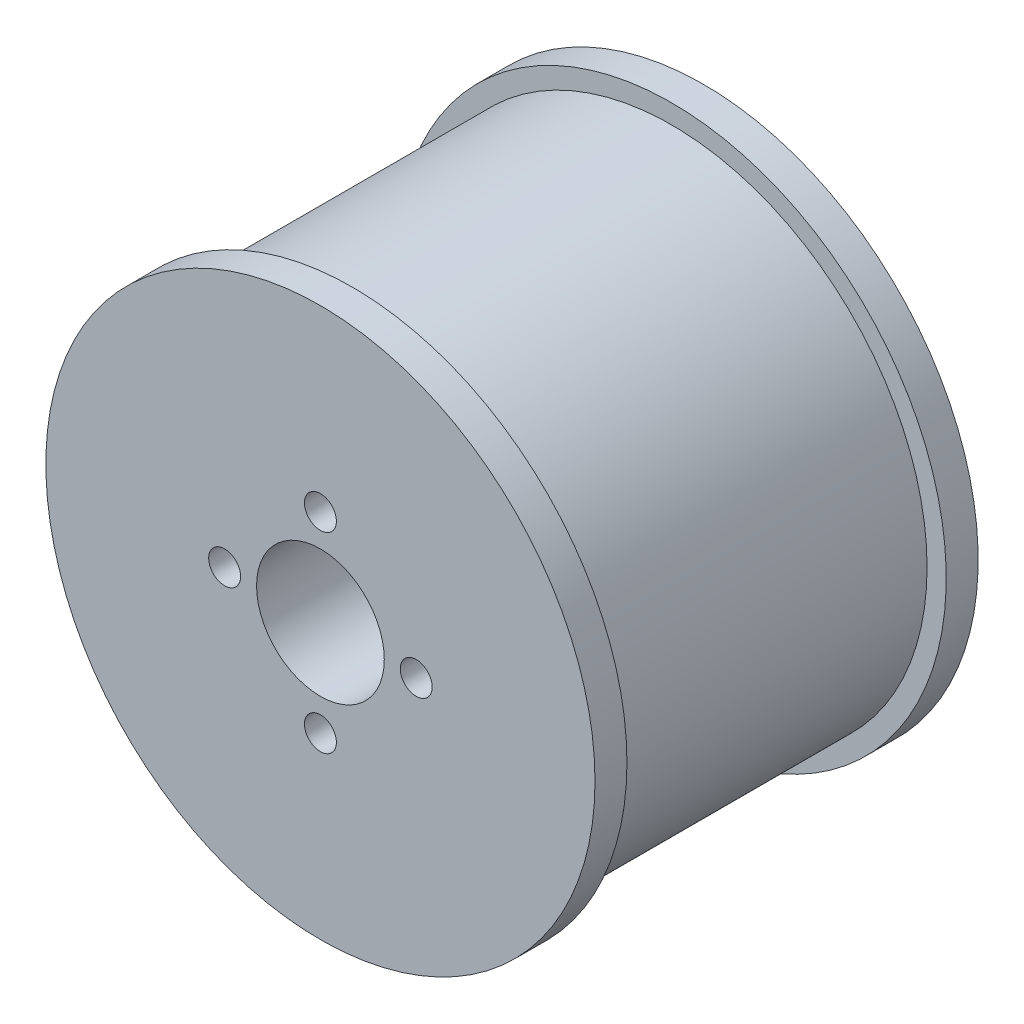
SolidWorks part; units mm, degrees
material "PET"
ref_plane "Front Plane" through (0, 0, 0) normal (0, 0, 1) x (1, 0, 0)
ref_plane "Top Plane" through (0, 0, 0) normal (0, 1, 0) x (1, 0, 0)
ref_plane "Right Plane" through (0, 0, 0) normal (1, 0, 0) x (0, 0, -1)
sketch "Sketch1" plane through (0, 0, 0) normal (0, 0, 1) x (1, 0, 0)
  circle A0 centre (0, 0) radius 40
  circle A1 centre (0, 0) radius 10
  dimension "D1" = 20
  dimension "D2" = 80
extrude "Boss-Extrude1" add sketch "Sketch1" along normal blind 50
sketch "Sketch2" plane through (0, 0, 50) normal (0, 0, 1) x (1, 0, 0)
  circle A0 centre (0, 0) radius 43
  circle A1 centre (0, 0) radius 40 construction
  circle A2 centre (0, 0) radius 10
  dimension "D1" = 3
  dimension "D2" = 20
extrude "Boss-Extrude2" add sketch "Sketch2" along normal blind 5
sketch "Sketch3" plane through (0, 0, 0) normal (0, 0, -1) x (-1, 0, 0)
  circle A0 centre (0, 0) radius 43
  circle A1 centre (0, 0) radius 43 construction
  circle A2 centre (0, 0) radius 10
  dimension "D1" = 20
extrude "Boss-Extrude3" add sketch "Sketch3" along normal blind 5
sketch "Sketch4" plane through (0, 0, 55) normal (0, 0, 1) x (1, 0, 0)
  circle A0 centre (0, 0) radius 15 construction
  circle A1 centre (0, 15) radius 2.5
  circle A2 centre (15, 0) radius 2.5
  circle A3 centre (0, -15) radius 2.5
  circle A4 centre (-15, 0) radius 2.5
  point P14 (0, 0)
  dimension "D1" = 30
  dimension "D2" = 5
  dimension "D3" = 4
extrude "Cut-Extrude1" cut sketch "Sketch4" against normal through all
